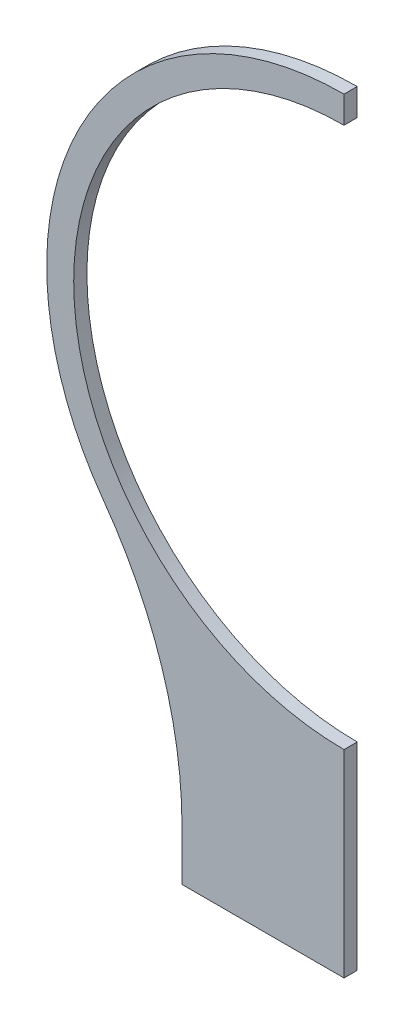
SolidWorks part; units mm, degrees
ref_plane "Front Plane" through (0, 0, 0) normal (0, 0, 1) x (1, 0, 0)
ref_plane "Top Plane" through (0, 0, 0) normal (0, 1, 0) x (1, 0, 0)
ref_plane "Right Plane" through (0, 0, 0) normal (1, 0, 0) x (0, 0, -1)
sketch "Sketch1" plane through (0, 0, 0) normal (0, 0, 1) x (1, 0, 0)
  line L0 (0, 130.023) -> (0, 143.0035)
  line L1 (0, -130.023) -> (0, -225.171)
  line L2 (0, -225.171) -> (-77.9257, -225.171)
  line L3 (-77.9257, -225.171) -> (-77.9257, -201.0192)
  arc A0 (0, 130.023) -> (0, -130.023) centre (0, 0) ccw
  arc A1 (0, 143.0035) -> (-115.8716, -83.808) centre (0, 0) ccw
  arc A2 (-115.8716, -83.808) -> (-77.9257, -201.0192) centre (-277.9257, -201.0192) cw
extrude "Boss-Extrude3" add sketch "Sketch1" along normal blind 6.35
